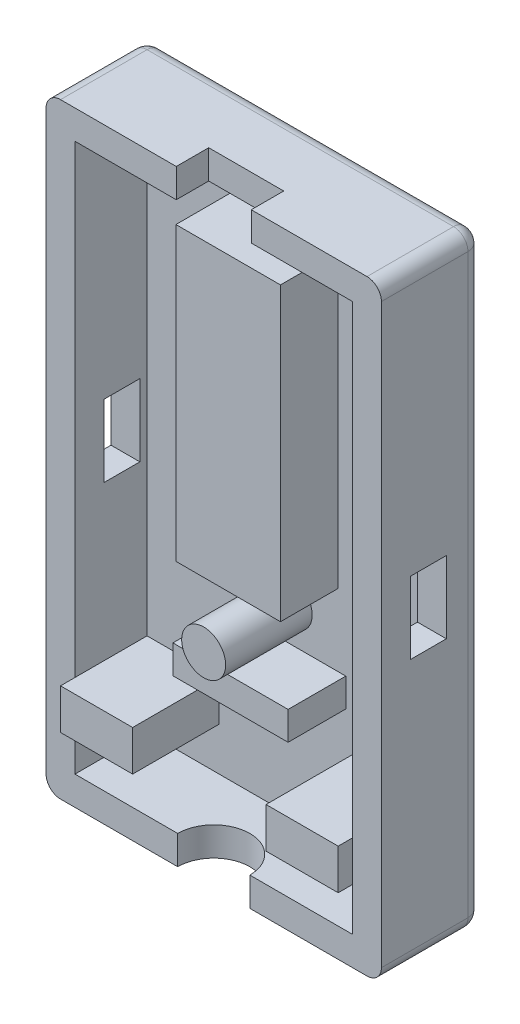
SolidWorks part; units mm, degrees
ref_plane "Front Plane" through (0, 0, 0) normal (0, 0, 1) x (1, 0, 0)
ref_plane "Top Plane" through (0, 0, 0) normal (0, 1, 0) x (1, 0, 0)
ref_plane "Right Plane" through (0, 0, 0) normal (1, 0, 0) x (0, 0, -1)
sketch "Sketch1" plane through (0, 0, 0) normal (0, 0, 1) x (1, 0, 0)
  line L1 (-11.625, 21) -> (11.625, 21)
  line L2 (-11.625, 21) -> (-11.625, -21)
  line L3 (-11.625, -21) -> (11.625, -21)
  line L4 (11.625, 21) -> (11.625, -21)
  point P0 (0, 0)
  dimension "D1" = 23.25
  dimension "D2" = 42
extrude "Boss-Extrude1" add sketch "Sketch1" along normal blind 2
sketch "Sketch2" plane through (0, 0, 2) normal (0, 0, 1) x (1, 0, 0)
  line L0 (11.625, 21) -> (-11.625, 21) construction
  line L1 (-11.625, 21) -> (11.625, 21)
  line L2 (-11.625, 21) -> (-11.625, -21)
  line L3 (-11.625, -21) -> (11.625, -21)
  line L4 (11.625, 21) -> (11.625, -21)
  line L5 (-11.625, 21) -> (-11.625, -21) construction
  line L11 (-9.625, 19) -> (9.625, 19)
  line L12 (-9.625, 19) -> (-9.625, -19)
  line L13 (-9.625, -19) -> (9.625, -19)
  line L14 (9.625, 19) -> (9.625, -19)
  dimension "D1" = 2
  dimension "D2" = 2
  dimension "D3" = 2
  dimension "D4" = 2
extrude "Boss-Extrude2" add sketch "Sketch2" along normal blind 5
sketch "Sketch3" plane through (0, 0, 2) normal (0, 0, 1) x (1, 0, 0)
  line L0 (0, 19) -> (0, 18)
  line L1 (9.625, 19) -> (-9.625, 19) construction
  line L2 (0, 18) -> (7.125, 18)
  line L3 (7.125, 18) -> (-7.125, 18)
  line L4 (-7.125, 18) -> (-7.125, -13)
  line L5 (-7.125, -13) -> (7.125, -13)
  line L6 (7.125, -13) -> (7.125, 18)
  line L7 (-7.125, -13) -> (-1.225, -13)
  line L8 (7.125, -13) -> (1.825, -13)
  line L9 (-7.125, -13) -> (-9.625, -13)
  line L14 (-9.625, 19) -> (-9.625, -19) construction
  line L15 (-9.625, -13.2) -> (-9.625, -16)
  line L16 (-9.625, -16) -> (-4.625, -16)
  line L17 (-4.625, -16) -> (-4.625, -13.2)
  line L18 (7.125, -13) -> (9.625, -13)
  line L19 (9.625, -19) -> (9.625, 19) construction
  line L20 (9.625, -13.2) -> (9.625, -16)
  line L21 (9.625, -16) -> (4.625, -16)
  line L22 (4.625, -16) -> (4.625, -13.2)
  line L23 (-4.625, -13) -> (-9.625, -13)
  line L24 (4.625, -13) -> (9.625, -13)
  line L25 (-9.625, -13) -> (-4.625, -13)
  line L26 (-4.625, -16) -> (-9.625, -16)
  line L27 (-9.625, -13) -> (9.625, -13)
  line L28 (9.625, -16) -> (4.625, -16)
  line L31 (-9.625, -13.2) -> (-4.625, -13.2)
  line L33 (4.625, -13.2) -> (9.625, -13.2)
  circle A0 centre (0.3, -6.225) radius 1.525
  line M5 (-9.625, 19) -> (-9.625, -19)
  line M7 (9.625, -19) -> (9.625, 19)
  dimension "D1" = 1
  dimension "D2" = 7.125
  dimension "D3" = 7.125
  dimension "D4" = 31
  dimension "D5" = 0.2
extrude "Boss-Extrude3" add sketch "Sketch3" along normal blind 6 contours A0 | L31 L16 L17 M5 | L33 L22 L21 M7
sketch "Sketch4" plane through (0, 0, 2) normal (0, 0, 1) x (1, 0, 0)
  line L0 (9.625, 19) -> (-9.625, 19) construction
  line L1 (-3.625, 16.5) -> (3.625, 16.5)
  line L2 (-3.625, 16.5) -> (-3.625, -3.725)
  line L3 (-3.625, -3.725) -> (3.625, -3.725)
  line L4 (3.625, 16.5) -> (3.625, -3.725)
  line L5 (-3.8345, -8.725) -> (4.154, -8.725)
  line L6 (-3.8345, -8.725) -> (-3.8345, -10.7)
  line L7 (-3.8345, -10.7) -> (4.154, -10.7)
  line L8 (4.154, -8.725) -> (4.154, -10.7)
  line L9 (4.625, -13.2) -> (9.625, -13.2) construction
  line L10 (9.625, -13.2) -> (9.625, 19) construction
  line L11 (-9.625, 19) -> (-9.625, -13.2) construction
  circle A1 centre (0.3, -6.225) radius 1.525 construction
  circle A3 centre (0.3, -6.225) radius 1.525 construction
  dimension "D1" = 2.5
  dimension "D2" = 2.5
  dimension "D3" = 2.5
  dimension "D4" = 2.5
  dimension "D5" = 6
  dimension "D6" = 6
extrude "Boss-Extrude4" add sketch "Sketch4" along normal blind 4
sketch "Sketch5" plane through (0, 19, 0) normal (0, -1, 0) x (1, 0, 0)
  line L0 (9.625, 7) -> (-9.625, 7) construction
  line L1 (-2.6, 9.25) -> (2.6, 9.25)
  line L2 (-2.6, 9.25) -> (-2.6, 4.75)
  line L3 (-2.6, 4.75) -> (2.6, 4.75)
  line L4 (2.6, 9.25) -> (2.6, 4.75)
  line L5 (-2.6, 9.25) -> (2.6, 4.75) construction
  line L6 (-2.6, 4.75) -> (2.6, 9.25) construction
  point P0 (0, 7)
  dimension "D1" = 4.5
  dimension "D2" = 5.2
extrude "Cut-Extrude1" cut sketch "Sketch5" against normal through all
sketch "Sketch6" plane through (0, -19, 0) normal (0, 1, 0) x (1, 0, 0)
  line L0 (-9.625, -7) -> (9.625, -7) construction
  line L1 (-2.5, -7) -> (2.5, -7)
  arc A0 (2.5, -7) -> (-2.5, -7) centre (0, -7) ccw
  dimension "D1" = 5
extrude "Cut-Extrude3" cut sketch "Sketch6" against normal through all
sketch "Sketch7" plane through (-9.625, 0, 0) normal (1, 0, 0) x (0, 0, -1)
  line L1 (-2.5, 0) -> (-2.5, 2.5)
  line L15 (-2.5, 0) -> (-2.5, -2.5)
  line L16 (-2.5, -2.5) -> (-5, -2.5)
  line L17 (-2.5, 2.5) -> (-5, 2.5)
  line L18 (-5, 2.5) -> (-5, -2.5)
  dimension "D1" = 2.5
  dimension "D2" = 2.5
  dimension "D3" = 2.5
extrude "Cut-Extrude4" cut sketch "Sketch7" against normal through all
sketch "Sketch8" plane through (9.625, 0, 0) normal (-1, 0, 0) x (0, 0, 1)
  line L7 (2.5, 0) -> (2.5, -2.5)
  line L8 (2.5, 0) -> (2.5, 2.5)
  line L9 (2.5, -2.5) -> (5, -2.5)
  line L10 (5, -2.5) -> (5, 2.5)
  line L11 (5, 2.5) -> (2.5, 2.5)
  dimension "D1" = 2.5
  dimension "D2" = 2.5
  dimension "D3" = 2.5
extrude "Cut-Extrude5" cut sketch "Sketch8" against normal through all
fillet "Fillet1" radius 1 8 edges at (-11.625, 21, 3.5) (0, 21, 0) (11.625, 21, 3.5) (11.625, 0, 0) (0, -21, 0) (-11.625, -21, 3.5) (-11.625, 0, 0) (11.625, -21, 3.5)
